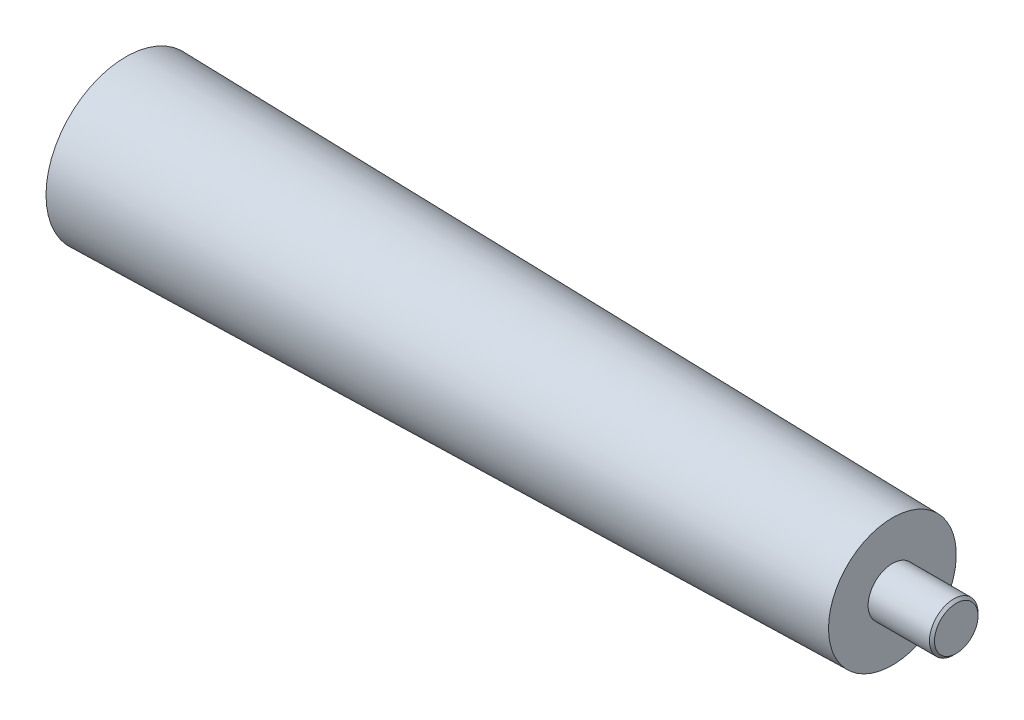
SolidWorks part; units mm, degrees
ref_plane "Front Plane" through (0, 0, 0) normal (0, 0, 1) x (1, 0, 0)
ref_plane "Top Plane" through (0, 0, 0) normal (0, 1, 0) x (1, 0, 0)
ref_plane "Right Plane" through (0, 0, 0) normal (1, 0, 0) x (0, 0, -1)
sketch "Sketch1" plane through (0, 0, 0) normal (0, 1, 0) x (1, 0, 0)
  line L0 (0, 0) -> (165.1, 0)
  line L1 (165.1, 0) -> (165.1, 4.83)
  line L2 (165.1, 4.83) -> (152.4, 4.83)
  line L3 (152.4, 4.83) -> (152.4, 12.7)
  line L4 (152.4, 12.7) -> (0, 15.88)
  line L5 (0, 15.88) -> (0, 0)
  dimension "D1" = 12.7
  dimension "D2" = 4.83
  dimension "D3" = 12.7
  dimension "D4" = 152.4
  dimension "D5" = 15.88
revolve "Revolve1" add sketch "Sketch1" angle 360 about L0
chamfer "Chamfer1" distance 0.5 angle 45 1 edges at (165.1, 0, 4.83)
